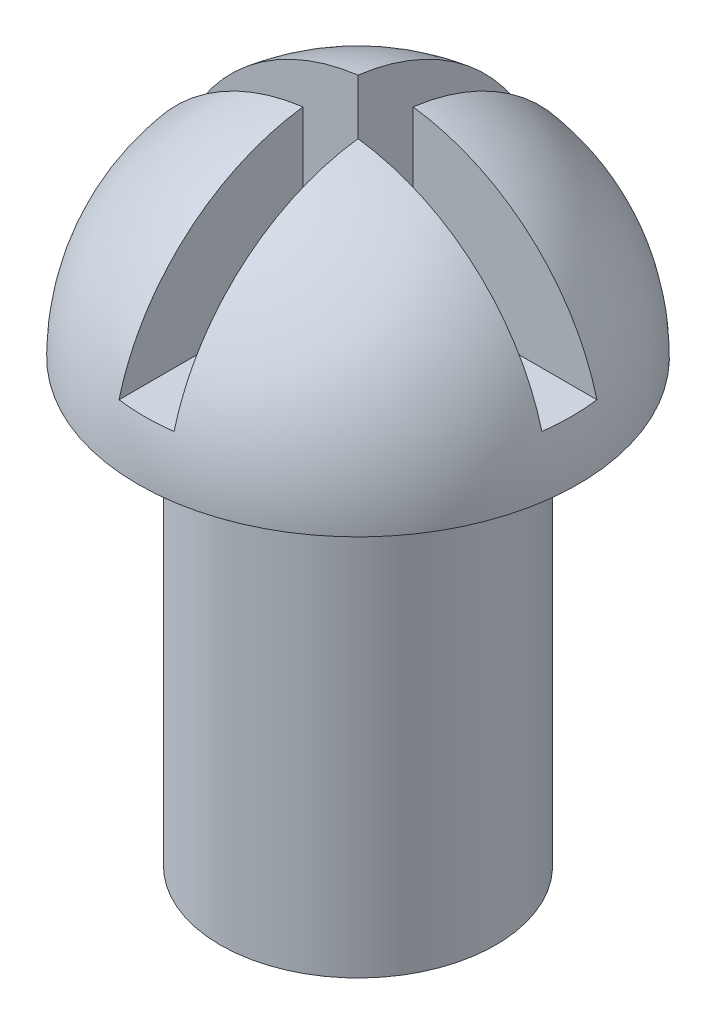
SolidWorks part; units mm, degrees
ref_plane "Front Plane" through (0, 0, 0) normal (0, 0, 1) x (1, 0, 0)
ref_plane "Top Plane" through (0, 0, 0) normal (0, 1, 0) x (1, 0, 0)
ref_plane "Right Plane" through (0, 0, 0) normal (1, 0, 0) x (0, 0, -1)
sketch "Sketch1" plane through (0, 0, 0) normal (0, 1, 0) x (1, 0, 0)
  circle A0 centre (0, 0) radius 2.5
  dimension "D1" = 5
extrude "Boss-Extrude1" add sketch "Sketch1" along normal blind 8
sketch "Sketch2" plane through (0, 8, 0) normal (0, 1, 0) x (1, 0, 0)
  line L0 (0, 4) -> (0, -4)
  arc A0 (0, -4) -> (0, 4) centre (0, 0) ccw
  dimension "D1" = 8
revolve "Revolve1" add sketch "Sketch2" angle 180 about L0
ref_plane "Plane1" through (0, 9, 0) normal (0, 1, 0) x (1, 0, 0)
sketch "Sketch3" plane through (0, 9, 0) normal (0, 1, 0) x (1, 0, 0)
  line L0 (0.5, 0.5) -> (5.63, 0.5)
  line L1 (-0.5, 4.674) -> (0.5, 4.674)
  line L2 (-0.5, 4.674) -> (-0.5, 0.5)
  line L3 (-0.5, -4.8333) -> (0.5, -4.8333)
  line L4 (0.5, 4.674) -> (0.5, 0.5)
  line L5 (-4.8333, 0.5) -> (-0.5, 0.5)
  line L6 (-4.8333, 0.5) -> (-4.8333, -0.5)
  line L7 (-4.8333, -0.5) -> (-0.5, -0.5)
  line L8 (5.63, 0.5) -> (5.63, -0.5)
  line L9 (-0.5, -0.5) -> (-0.5, -4.8333)
  line L10 (0.5, -0.5) -> (5.63, -0.5)
  line L11 (0.5, -0.5) -> (0.5, -4.8333)
  dimension "D1" = 1
  dimension "D2" = 0.5
  dimension "D3" = 1
  dimension "D4" = 0.5
extrude "Cut-Extrude1" cut sketch "Sketch3" along normal blind 3
